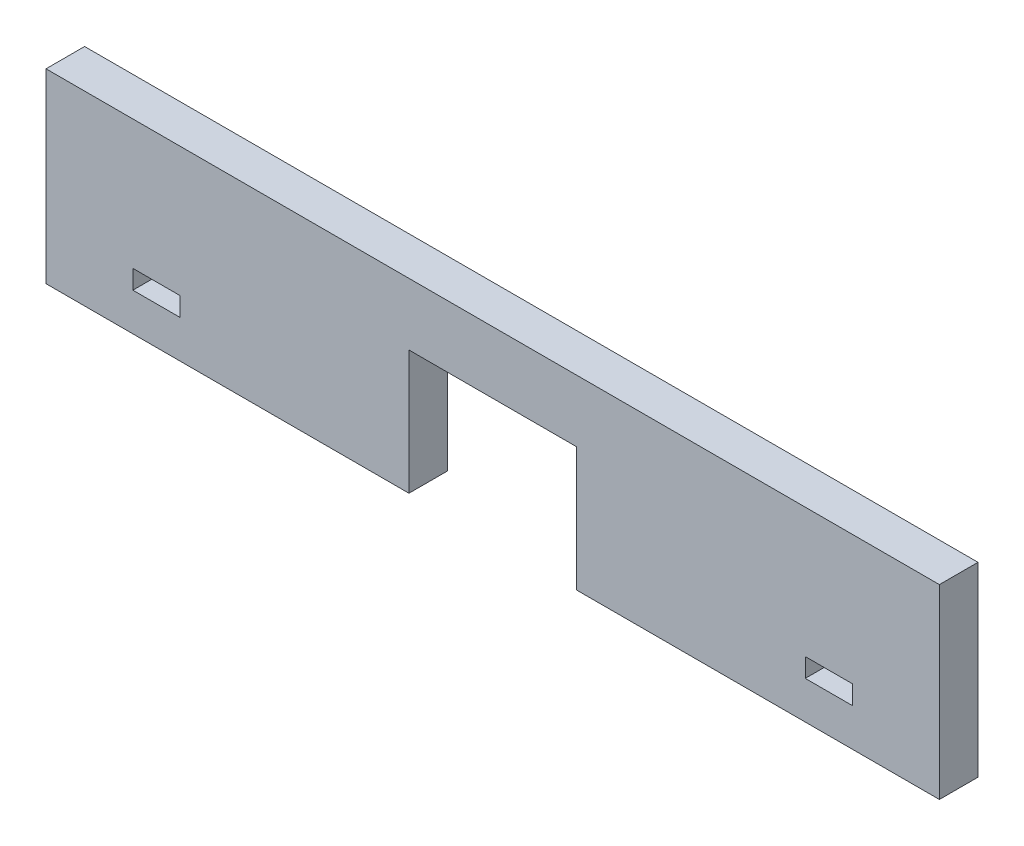
SolidWorks part; units mm, degrees
ref_plane "정면" through (0, 0, 0) normal (0, 0, 1) x (1, 0, 0)
ref_plane "윗면" through (0, 0, 0) normal (0, 1, 0) x (1, 0, 0)
ref_plane "우측면" through (0, 0, 0) normal (1, 0, 0) x (0, 0, -1)
sketch "Sketch1" plane through (0, 0, 0) normal (0, 0, 1) x (1, 0, 0)
  line L0 (-36.0174, -7.5914) -> (-6.7674, -7.5914)
  line L1 (-36.0174, -7.5914) -> (-36.0174, -5.0914)
  line L2 (-36.0174, 7.4086) -> (35.9826, 7.4086)
  line L3 (35.9826, -7.5914) -> (35.9826, -5.0914)
  line L4 (-36.0174, 4.9086) -> (-36.0174, 7.4086)
  line L5 (35.9826, 4.9086) -> (35.9826, 7.4086)
  line L6 (-6.7674, 2.4086) -> (6.7326, 2.4086)
  line L7 (-6.7674, 2.4086) -> (-6.7674, -7.5914)
  line L8 (6.7326, 2.4086) -> (6.7326, -7.5914)
  line L9 (-36.0174, 4.9086) -> (-36.0174, -5.0914)
  line L10 (35.9826, 4.9086) -> (35.9826, -5.0914)
  line L11 (-36.0174, -7.5914) -> (-34.0174, -7.5914) construction
  line L12 (25.1726, -4.5434) -> (25.1726, -3.0194)
  line L13 (-29.0174, -4.5434) -> (-25.2074, -4.5434)
  line L14 (-29.0174, -4.5434) -> (-29.0174, -3.0194)
  line L15 (-29.0174, -3.0194) -> (-25.2074, -3.0194)
  line L16 (-25.2074, -4.5434) -> (-25.2074, -3.0194)
  line L17 (28.9826, -3.0194) -> (25.1726, -3.0194)
  line L18 (28.9826, -4.5434) -> (28.9826, -3.0194)
  line L19 (28.9826, -4.5434) -> (25.1726, -4.5434)
  line L20 (6.7326, -7.5914) -> (35.9826, -7.5914)
  dimension "D1" = 7
  dimension "D2" = 7
  dimension "D3" = 72
extrude "Boss-Extrude1" add sketch "Sketch1" along normal blind 3.1115
